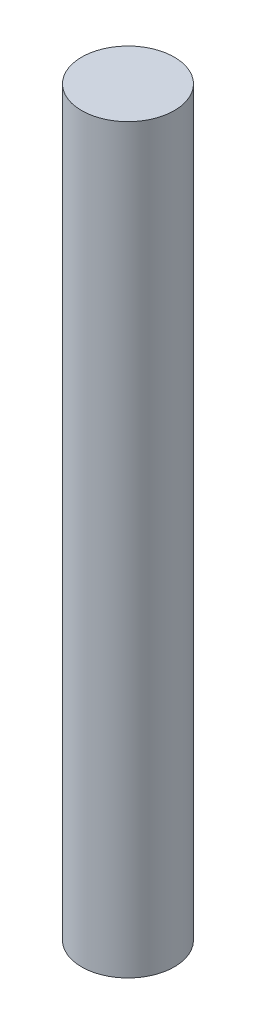
SolidWorks part; units mm, degrees
material "201 Acero inoxidable recocido (SS)"
ref_plane "Alzado" through (0, 0, 0) normal (0, 0, 1) x (1, 0, 0)
ref_plane "Planta" through (0, 0, 0) normal (0, 1, 0) x (1, 0, 0)
ref_plane "Vista lateral" through (0, 0, 0) normal (1, 0, 0) x (0, 0, -1)
sketch "Croquis1" plane through (0, 0, 0) normal (0, 1, 0) x (1, 0, 0)
  circle A0 centre (0, 0) radius 12.5
  dimension "D1" = 25
extrude "Saliente-Extruir1" add sketch "Croquis1" along normal blind 200
